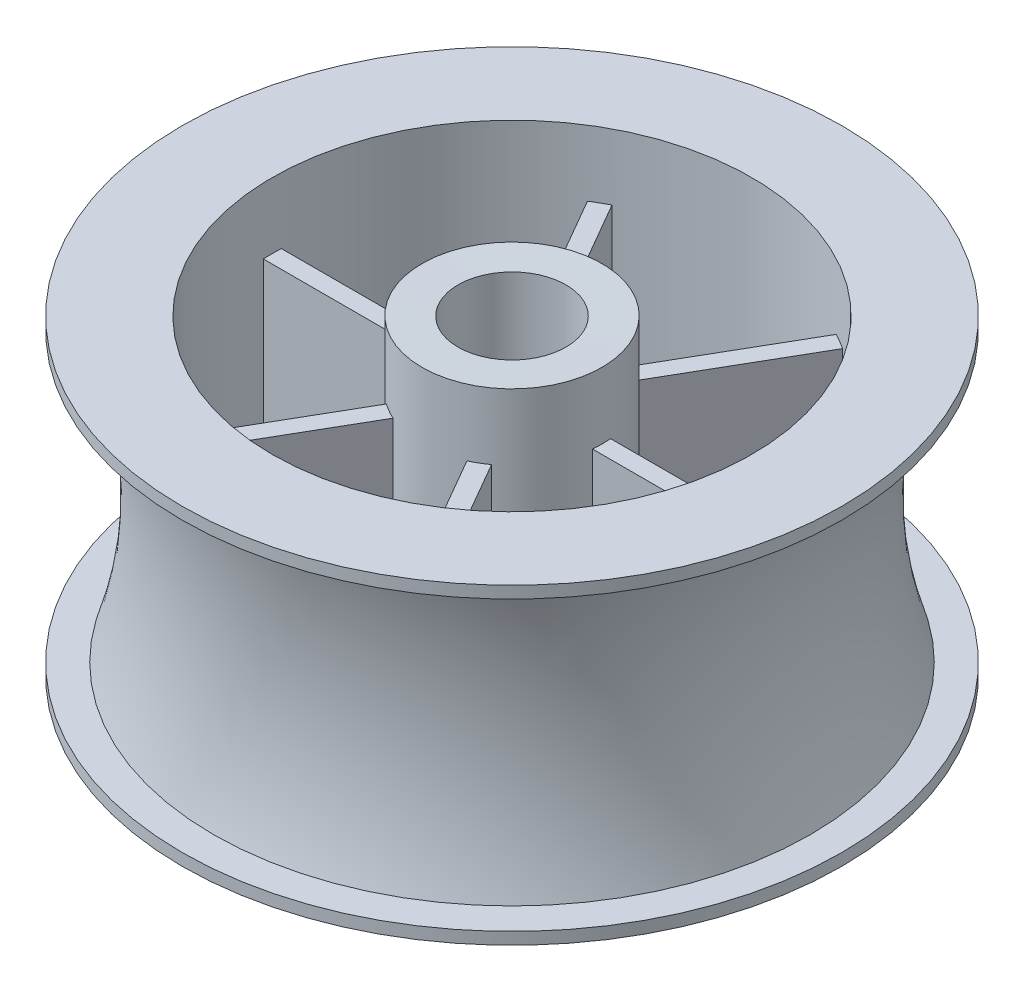
SolidWorks part; units mm, degrees
ref_plane "Front Plane" through (0, 0, 0) normal (0, 0, 1) x (1, 0, 0)
ref_plane "Top Plane" through (0, 0, 0) normal (0, 1, 0) x (1, 0, 0)
ref_plane "Right Plane" through (0, 0, 0) normal (1, 0, 0) x (0, 0, -1)
sketch "Sketch1" plane through (0, 0, 0) normal (0, 0, 1) x (1, 0, 0)
  line L9 (-20, 26) -> (-27.5, 26)
  line L12 (0, -55) -> (0, 55) construction
  line L14 (-27.5, 26) -> (-27.5, 25)
  line L15 (-27.5, 25) -> (-24.9, 25)
  line L16 (0, 42.4047) -> (0, -19.2024) construction
  line L17 (-24.9, 1) -> (-27.5, 1)
  line L18 (-27.5, 1) -> (-27.5, 0)
  line L19 (55, 0) -> (-55, 0) construction
  line L20 (-27.5, 0) -> (-20, 0)
  line L21 (-20, 26) -> (-20, 20.5)
  line L22 (-4.5, 26) -> (-4.5, 0)
  line L23 (-4.5, 0) -> (-7.5, 0)
  line L24 (-7.5, 0) -> (-7.5, 5.5)
  line L25 (-7.5, 26.0371) -> (-4.5, 26)
  line L28 (-20, 5.5) -> (-20, 0)
  line L29 (-7.5, 20.5) -> (-7.5, 26.0371)
  line L30 (-20, 20.5) -> (-20, 5.5)
  line L31 (-7.5, 20.5) -> (-7.5, 5.5)
  arc A1 (-24.9, 1) -> (-24.9, 25) centre (-63.0576, 13) ccw
  dimension "D6" = 40
  dimension "D1" = 20
  dimension "D2" = 27.5
  dimension "D3" = 1
  dimension "D4" = 2.6
  dimension "D5" = 1
  dimension "D7" = 2.6
  dimension "D8" = 27.5
  dimension "D9" = 26
  dimension "D10" = 9
  dimension "D11" = 15
  dimension "D12" = 5.5
  dimension "D13" = 5.5
revolve "Revolve1" add sketch "Sketch1" angle 360 about L16
sketch "Sketch4" plane through (0, 0, 0) normal (0, 1, 0) x (1, 0, 0)
  line L0 (6.834, 0.75) -> (20.4487, 0.75)
  line L1 (20.4487, 0.75) -> (20.4487, -0.75)
  line L2 (20.4487, -0.75) -> (6.834, -0.75)
  line L3 (6.834, -0.75) -> (6.834, 0.75)
  line L4 (-14.3204, 0) -> (14.3204, 0) construction
  line L5 (0, -35.786) -> (0, 35.8272) construction
  line L6 (-30.9916, -17.893) -> (31.0273, 17.9136) construction
  line L7 (4.0665, -5.5435) -> (10.8739, -17.3341)
  line L8 (9.5748, -18.0841) -> (2.7675, -6.2935)
  line L9 (2.7675, -6.2935) -> (4.0665, -5.5435)
  line L10 (10.8739, -17.3341) -> (9.5748, -18.0841)
  line L11 (-30.9916, 17.893) -> (31.0273, -17.9136) construction
  line L12 (-2.7675, -6.2935) -> (-9.5748, -18.0841)
  line L13 (-10.8739, -17.3341) -> (-4.0665, -5.5435)
  line L14 (-4.0665, -5.5435) -> (-2.7675, -6.2935)
  line L15 (-9.5748, -18.0841) -> (-10.8739, -17.3341)
  line L16 (0, 35.786) -> (0, -35.8272) construction
  line L17 (-6.834, -0.75) -> (-20.4487, -0.75)
  line L18 (-20.4487, 0.75) -> (-6.834, 0.75)
  line L19 (-6.834, 0.75) -> (-6.834, -0.75)
  line L20 (-20.4487, -0.75) -> (-20.4487, 0.75)
  line L21 (30.9916, 17.893) -> (-31.0273, -17.9136) construction
  line L22 (-4.0665, 5.5435) -> (-10.8739, 17.3341)
  line L23 (-9.5748, 18.0841) -> (-2.7675, 6.2935)
  line L24 (-2.7675, 6.2935) -> (-4.0665, 5.5435)
  line L25 (-10.8739, 17.3341) -> (-9.5748, 18.0841)
  line L26 (30.9916, -17.893) -> (-31.0273, 17.9136) construction
  line L27 (2.7675, 6.2935) -> (9.5748, 18.0841)
  line L28 (10.8739, 17.3341) -> (4.0665, 5.5435)
  line L29 (4.0665, 5.5435) -> (2.7675, 6.2935)
  line L30 (9.5748, 18.0841) -> (10.8739, 17.3341)
  point P42 (0, 0)
  dimension "D1" = 1.5
  dimension "D2" = 0.75
  dimension "D3" = 6
extrude "Boss-Extrude1" add sketch "Sketch4" along normal blind 15 from offset 5.5
